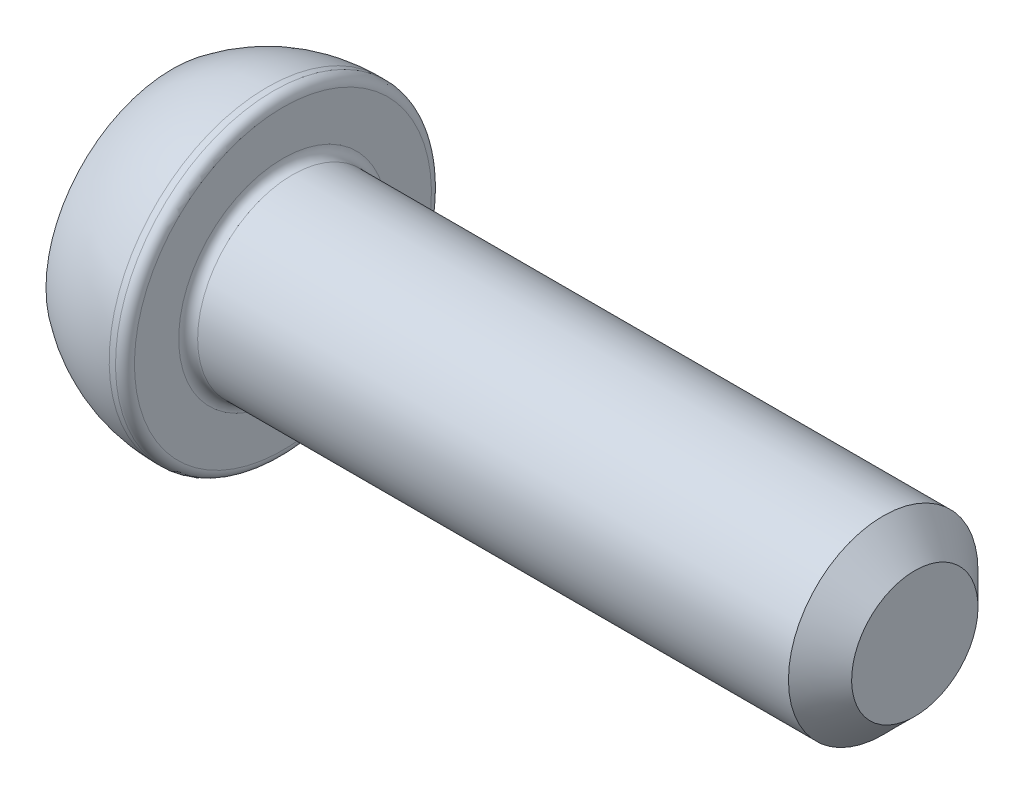
SolidWorks part; units mm, degrees
ref_plane "Спереди" through (0, 0, 0) normal (0, 0, 1) x (1, 0, 0)
ref_plane "Сверху" through (0, 0, 0) normal (0, 1, 0) x (1, 0, 0)
ref_plane "Справа" through (0, 0, 0) normal (1, 0, 0) x (0, 0, -1)
sketch "Эскиз1" plane through (0, 0, 0) normal (0, 0, 1) x (1, 0, 0)
  line L0 (0, 0) -> (0, 4)
  line L1 (3, 5) -> (3.5, 5)
  line L2 (3.5, 5) -> (3.5, 3)
  line L3 (3.5, 3) -> (23.5, 3)
  line L4 (23.5, 3) -> (23.5, 0)
  line L5 (23.5, 0) -> (0, 0) construction
  line L6 (0, 0) -> (23.5, 0)
  arc A0 (0, 4) -> (3, 5) centre (3, 0) cw
  point P9 (3.5, 4)
  dimension "D1" = 0.5
  dimension "D2" = 6
  dimension "D3" = 10
  dimension "D5" = 3.5
  dimension "D6" = 20
revolve "Повернуть1" add sketch "Эскиз1" angle 360 about L5
cosmetic thread "Условное изображение резьбы1" parameters "D2"=4.891
sketch "Эскиз2" plane through (0, 0, 0) normal (-1, 0, 0) x (0, 0, 1)
  line L1 (1.1547, 2) -> (-1.1547, 2)
  line L2 (-1.1547, 2) -> (-2.3094, 0)
  line L3 (-2.3094, 0) -> (-1.1547, -2)
  line L4 (-1.1547, -2) -> (1.1547, -2)
  line L5 (1.1547, -2) -> (2.3094, 0)
  line L6 (2.3094, 0) -> (1.1547, 2)
  circle A0 centre (0, 0) radius 2 construction
  dimension "D1" = 4
extrude "Вырез-Вытянуть1" cut sketch "Эскиз2" against normal blind 2
fillet "Скругление1" radius 0.3 2 edges at (3.5, 3, 0) (3.5, 5, 0)
chamfer "Фаска1" distance 1 angle 45 1 edges at (23.5, 3, 0)
